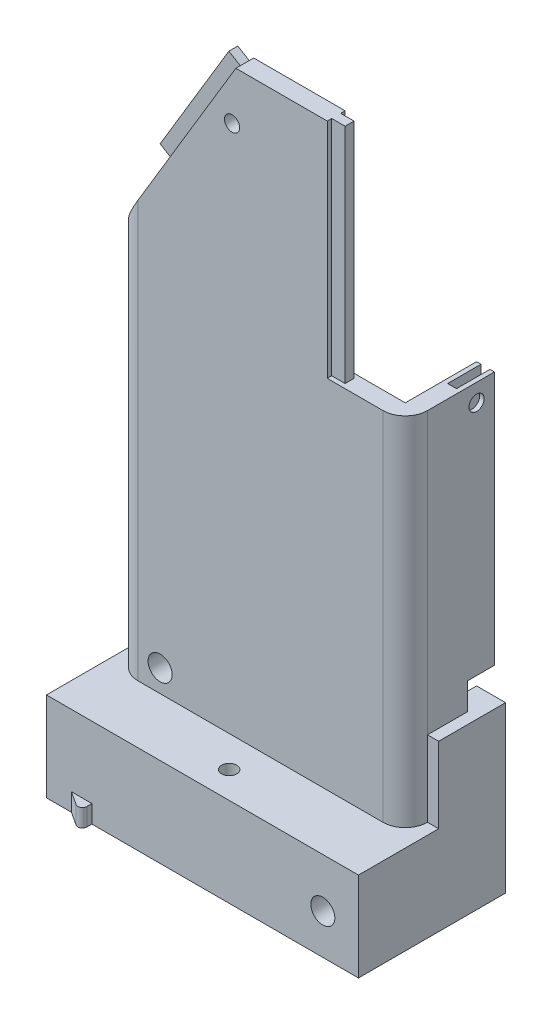
SolidWorks part; units mm, degrees
other "Markup1"
sketch "Sketch49" plane through (-35, -18, -2) normal (0, 0, -1) x (-1, 0, 0)
ref_plane "Front Plane" through (0, 0, 0) normal (0, 0, 1) x (1, 0, 0)
ref_plane "Top Plane" through (0, 0, 0) normal (0, 1, 0) x (1, 0, 0)
ref_plane "Right Plane" through (0, 0, 0) normal (1, 0, 0) x (0, 0, -1)
sketch "Sketch1" plane through (0, 0, 0) normal (0, 1, 0) x (1, 0, 0)
  line L1 (-32.5, -20) -> (32.5, -20)
  line L2 (-32.5, -20) -> (-32.5, 20)
  line L3 (-32.5, 20) -> (32.5, 20)
  line L4 (32.5, -20) -> (32.5, 20)
  line L5 (-32.5, -20) -> (32.5, 20) construction
  line L6 (-32.5, 20) -> (32.5, -20) construction
  point P0 (0, 0)
  dimension "D1" = 65
  dimension "D2" = 40
extrude "Boss-Extrude1" add sketch "Sketch1" along normal blind 130
shell "Shell1" thickness 4
fillet "Fillet1" radius 5 4 edges at (32.5, 65, -20) (32.5, 65, 20) (-32.5, 65, -20) (-32.5, 65, 20)
sketch "Sketch2" plane through (0, 0, 0) normal (0, 0, 1) x (1, 0, 0)
  line L0 (-5.5, 130) -> (-32.5, 85)
  line L1 (28.5, 130) -> (-28.5, 130) construction
  line L2 (-32.5, 130) -> (-32.5, 0) construction
  line L3 (-32.5, 85) -> (-32.5, 130)
  line L4 (-32.5, 130) -> (-5.5, 130)
  dimension "D1" = 5.5
  dimension "D2" = 85
extrude "Cut-Extrude1" cut sketch "Sketch2" against normal through all both and the other way through all
sketch "Sketch3" plane through (0, 0, 0) normal (0, 0, 1) x (1, 0, 0)
  line L1 (32.5, 130) -> (15, 130)
  line L2 (32.5, 130) -> (32.5, 80)
  line L3 (32.5, 80) -> (15, 80)
  line L4 (15, 130) -> (15, 80)
  dimension "D1" = 50
  dimension "D2" = 17.5
extrude "Cut-Extrude2" cut sketch "Sketch3" against normal through all both and the other way through all
sketch "Sketch5" plane through (15, 0, 0) normal (1, 0, 0) x (0, 0, -1)
  line L0 (-18, 130) -> (-18, 80) construction
  line L1 (-16, 130) -> (-20, 130) construction
  line L2 (-16, 80) -> (-20, 80) construction
  line L4 (-19, 130) -> (-17, 130)
  line L5 (-19, 130) -> (-19, 80)
  line L6 (-19, 80) -> (-17, 80)
  line L7 (-17, 130) -> (-17, 80)
  dimension "D1" = 2
extrude "Boss-Extrude2" add sketch "Sketch5" along normal blind 3
mirror "Mirror1" about plane through (0, 0, 0) normal (0, 0, 1) of "Boss-Extrude2"
sketch "Sketch6" plane through (-61.3971, 36.8382, 0) normal (-0.8575, 0.5145, 0) x (0, 0, 1)
  line L0 (-18, 108.6444) -> (-18, 78.6444) construction
  line L1 (-20, 108.6444) -> (-16, 108.6444) construction
  line L3 (-19, 108.6444) -> (-17, 108.6444)
  line L4 (-19, 108.6444) -> (-19, 78.6444)
  line L5 (-19, 78.6444) -> (-17, 78.6444)
  line L6 (-17, 108.6444) -> (-17, 78.6444)
  dimension "D1" = 30
  dimension "D2" = 2
extrude "Boss-Extrude3" add sketch "Sketch6" along normal blind 3
mirror "Mirror2" about plane through (0, 0, 0) normal (0, 0, 1) of "Boss-Extrude3"
sketch "Sketch8" plane through (0, 0, 0) normal (0, 1, 0) x (1, 0, 0)
  line L1 (-35, -33) -> (35, -33)
  line L2 (-35, -33) -> (-35, 33)
  line L3 (-35, 33) -> (35, 33)
  line L4 (35, -33) -> (35, 33)
  line L5 (-35, -33) -> (35, 33) construction
  line L6 (-35, 33) -> (35, -33) construction
  point P0 (0, 0)
  dimension "D1" = 66
  dimension "D2" = 70
extrude "Boss-Extrude4" add sketch "Sketch8" against normal blind 20
sketch "Sketch10" plane through (-35, 0, 0) normal (-1, 0, 0) x (0, 0, 1)
  line L0 (-33, -10) -> (33, -10) construction
  line L1 (-30, -16) -> (30, -16)
  line L2 (-30, -16) -> (-30, -4)
  line L3 (-30, -4) -> (30, -4)
  line L4 (30, -16) -> (30, -4)
  line L5 (-30, -16) -> (30, -4) construction
  line L6 (-30, -4) -> (30, -16) construction
  line L7 (-33, -20) -> (-33, 0) construction
  line L8 (33, -20) -> (33, 0) construction
  line L9 (0, 0) -> (0, -20) construction
  line L10 (-33, -20) -> (33, -20) construction
  point P0 (0, -10)
  dimension "D1" = 60
  dimension "D2" = 12
extrude "Cut-Extrude4" cut sketch "Sketch10" against normal blind 45
sketch "Sketch23" plane through (0, 80, 0) normal (0, 1, 0) x (1, 0, 0)
  line L0 (0, 0) -> (32.5, 0) construction
  line L1 (29.5, 7.5) -> (31.5, 7.5)
  line L2 (29.5, 7.5) -> (29.5, -7.5)
  line L3 (29.5, -7.5) -> (31.5, -7.5)
  line L4 (31.5, 7.5) -> (31.5, -7.5)
  line L5 (32.5, 15) -> (32.5, -15) construction
  line L6 (28.5, 16) -> (28.5, -16) construction
  line L8 (30.5, 14.75) -> (30.5, -14.75) construction
  dimension "D1" = 2
  dimension "D2" = 15
extrude "Cut-Extrude10" cut sketch "Sketch23" against normal blind 10
sketch "Sketch24" plane through (32.5, 0, 0) normal (1, 0, 0) x (0, 0, -1)
  line L1 (15, 80) -> (-15, 80) construction
  circle A0 centre (-4, 76) radius 1.7
  point P2 (0, 80)
  dimension "D3" = 3.4
  dimension "D1" = 4
  dimension "D2" = 4
extrude "Cut-Extrude11" cut sketch "Sketch24" against normal blind 10 and the other way through all
mirror "Mirror4" about plane through (0, 0, 0) normal (0, 0, 1) of "Cut-Extrude11"
sketch "Sketch27" plane through (0, 0, 0) normal (0, 1, 0) x (1, 0, 0)
  line L0 (35, -33) -> (35, 33) construction
  line L1 (-35, 33) -> (35, 33)
  line L2 (-35, 33) -> (-35, 0)
  line L3 (-35, 0) -> (35, 0)
  line L4 (35, 33) -> (35, 0)
extrude "Cut-Extrude12" cut sketch "Sketch27" against normal through all both and the other way through all
sketch "Sketch31" plane through (0, 0, 33) normal (0, 0, 1) x (1, 0, 0)
  line L0 (35, -20) -> (35, 0) construction
  line L1 (-35, -20) -> (35, -20) construction
  circle A0 centre (27, -11) radius 2.7
  dimension "D1" = 5.4
  dimension "D2" = 8
  dimension "D3" = 9
extrude "Cut-Extrude13" cut sketch "Sketch31" against normal through all both and the other way through all
sketch "Sketch34" plane through (0, 0, 0) normal (0, 1, 0) x (1, 0, 0)
  line L1 (-35, 0) -> (-35, -33) construction
  line L2 (-35, -33) -> (35, -33) construction
  circle A0 centre (0, -27) radius 1.7
  dimension "D1" = 3.4
  dimension "D2" = 6
  dimension "D3" = 35
extrude "Cut-Extrude15" cut sketch "Sketch34" against normal through all both and the other way through all
sketch "Sketch37" plane through (32.5, 0, 0) normal (1, 0, 0) x (0, 0, -1)
  line L0 (0, 0) -> (0, 80) construction
  line L1 (0, 23) -> (-6, 23)
  line L2 (0, 23) -> (0, 17)
  line L3 (0, 17) -> (-6, 17)
  line L4 (-6, 23) -> (-6, 17)
  line L5 (-15, 0) -> (0, 0) construction
  dimension "D1" = 6
  dimension "D2" = 6
  dimension "D3" = 17
extrude "Cut-Extrude17" cut sketch "Sketch37" against normal through all both and the other way through all
sketch "Sketch38" plane through (32.5, 0, 0) normal (1, 0, 0) x (0, 0, -1)
  line L1 (0, 17) -> (-15, 17)
  line L2 (0, 17) -> (0, 0)
  line L3 (0, 0) -> (-15, 0)
  line L4 (-15, 17) -> (-15, 0)
extrude "Boss-Extrude9" add sketch "Sketch38" along normal up to surface (2.5 mm away) up to face at (35, -10, 16.5)
sketch "Sketch41" plane through (0, -20, 0) normal (0, -1, 0) x (-1, 0, 0)
  circle A0 centre (0, -27) radius 4
  dimension "D1" = 8
extrude "Cut-Extrude18" cut sketch "Sketch41" against normal blind 2.4
sketch "Sketch42" plane through (0, 0, 33) normal (0, 0, 1) x (1, 0, 0)
  line L0 (-35, -10) -> (35, -10) construction
  line L1 (-35, -20) -> (-35, 0) construction
  line L2 (35, -20) -> (35, 0) construction
  line L3 (-35, -20) -> (35, -20) construction
  line L4 (-29.4, -16) -> (-24.8, -16)
  line L5 (-29.4, -16) -> (-29.4, -20)
  line L6 (-29.4, -20) -> (-24.8, -20)
  line L7 (-24.8, -16) -> (-24.8, -20)
  dimension "D1" = 4
  dimension "D2" = 4.6
  dimension "D3" = 5.6
extrude "Boss-Extrude10" add sketch "Sketch42" along normal blind 3
sketch "Sketch43" plane through (0, -16, 0) normal (0, 1, 0) x (1, 0, 0)
  line L0 (-24.8, -36) -> (-29.4, -33)
  line L1 (-29.4, -33) -> (-29.4, -36)
  line L2 (-29.4, -36) -> (-24.8, -36)
extrude "Cut-Extrude19" cut sketch "Sketch43" against normal through all contours L2 L0 L1
fillet "Fillet2" radius 1 1 edges at (-24.8, -18, 36)
sketch "Sketch46" plane through (0, 0, 20) normal (0, 0, 1) x (1, 0, 0)
  line L0 (-27.5, 93.3333) -> (-5.5, 130) construction
  line L1 (-6.3575, 118.8526) -> (-10.645, 121.4251) construction
  line L2 (-5.5, 130) -> (-20.9349, 104.2752) construction
  circle A0 centre (-6.3575, 118.8526) radius 1.7
  dimension "D1" = 5
  dimension "D2" = 3.4
  dimension "D3" = 10
  dimension "D4" = 5
extrude "Cut-Extrude20" cut sketch "Sketch46" against normal blind 10
sketch "Sketch50" plane through (0, 0, 16) normal (0, 0, -1) x (-1, 0, 0)
  line L1 (13.5, 0) -> (28.5, 0)
  line L2 (13.5, 0) -> (13.5, 15)
  line L3 (13.5, 15) -> (28.5, 15)
  line L4 (28.5, 0) -> (28.5, 15)
  point P5 (0, 0)
  dimension "D1" = 15
  dimension "D2" = 15
extrude "Boss-Extrude11" add sketch "Sketch50" along normal up to surface (16 mm away) up to face at (-30.5, 55.6667, 0)
sketch "Sketch51" plane through (0, 0, 20) normal (0, 0, 1) x (1, 0, 0)
  line L0 (-27.5, 0) -> (27.5, 0) construction
  line L2 (-27.5, 93.3333) -> (-27.5, 0) construction
  circle A0 centre (-22.5, 5) radius 2.7
  dimension "D3" = 5.4
  dimension "D1" = 5
  dimension "D2" = 5
extrude "Cut-Extrude21" cut sketch "Sketch51" against normal through all both and the other way through all
